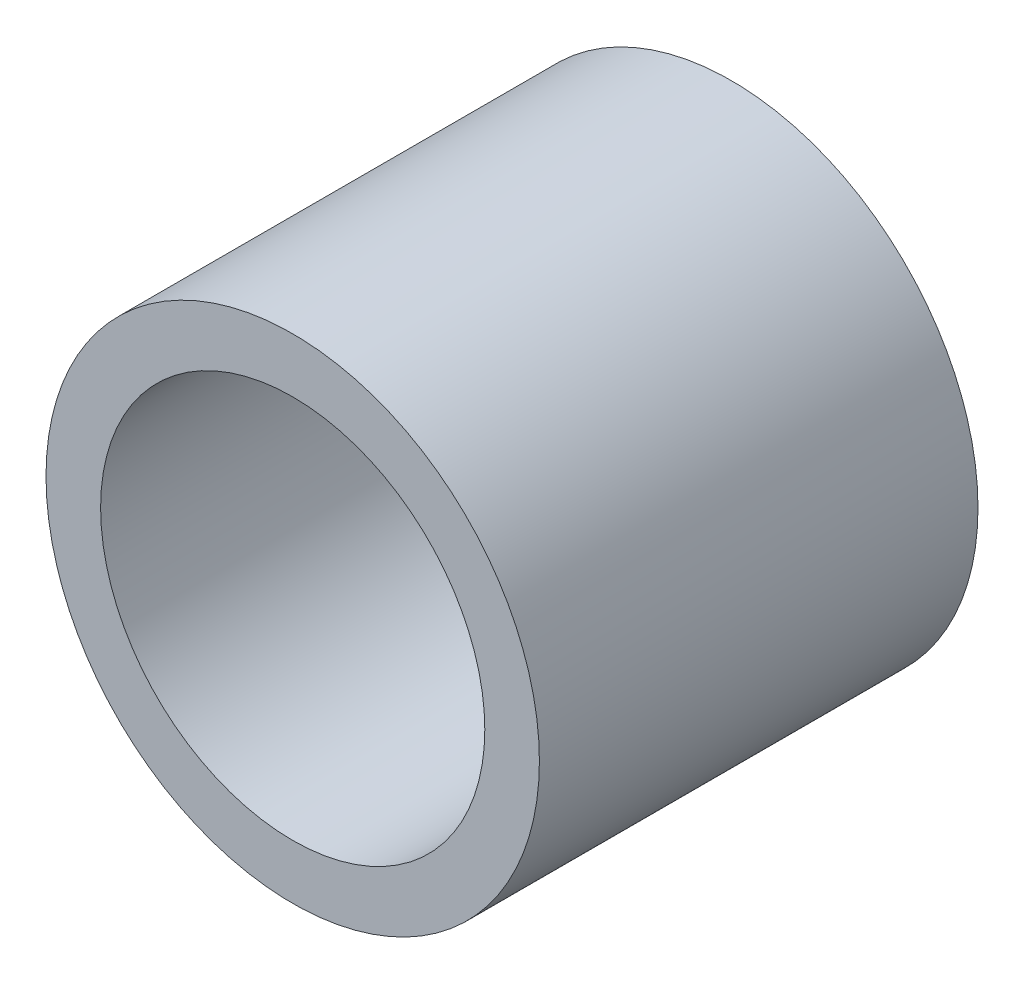
SolidWorks part; units mm, degrees
material "Tin Bearing Bronze"
ref_plane "Front Plane" through (0, 0, 0) normal (0, 0, 1) x (1, 0, 0)
ref_plane "Top Plane" through (0, 0, 0) normal (0, 1, 0) x (1, 0, 0)
ref_plane "Right Plane" through (0, 0, 0) normal (1, 0, 0) x (0, 0, -1)
sketch "Sketch1" plane through (0, 0, 0) normal (0, 0, 1) x (1, 0, 0)
  circle A0 centre (0, 0) radius 14.2875
  circle A1 centre (0, 0) radius 11.1252
  dimension "D1" = 28.575
  dimension "ID" = 22.2504
extrude "Extrude1" add sketch "Sketch1" along normal mid plane 25.4
sketch "Sketch2" plane through (0, 0, 0) normal (1, 0, 0) x (0, 0, -1)
  line L0 (-12.7, -11.1252) -> (12.7, -11.1252) construction
  line L3 (12.7, 11.1252) -> (-12.7, 11.1252) construction
  line L5 (-12.7, -11.1252) -> (12.7, -11.1252)
  line L6 (12.7, 11.1252) -> (-12.7, 11.1252)
sketch "Sketch4" plane through (0, 0, 12.7) normal (0, 0, 1) x (1, 0, 0)
  line L0 (0, 0) -> (-7.8667, 7.8667)
  line L1 (0, -48.895) -> (0, 48.895) construction
  circle A0 centre (0, 0) radius 11.1252 construction
  dimension "D1" = 45
